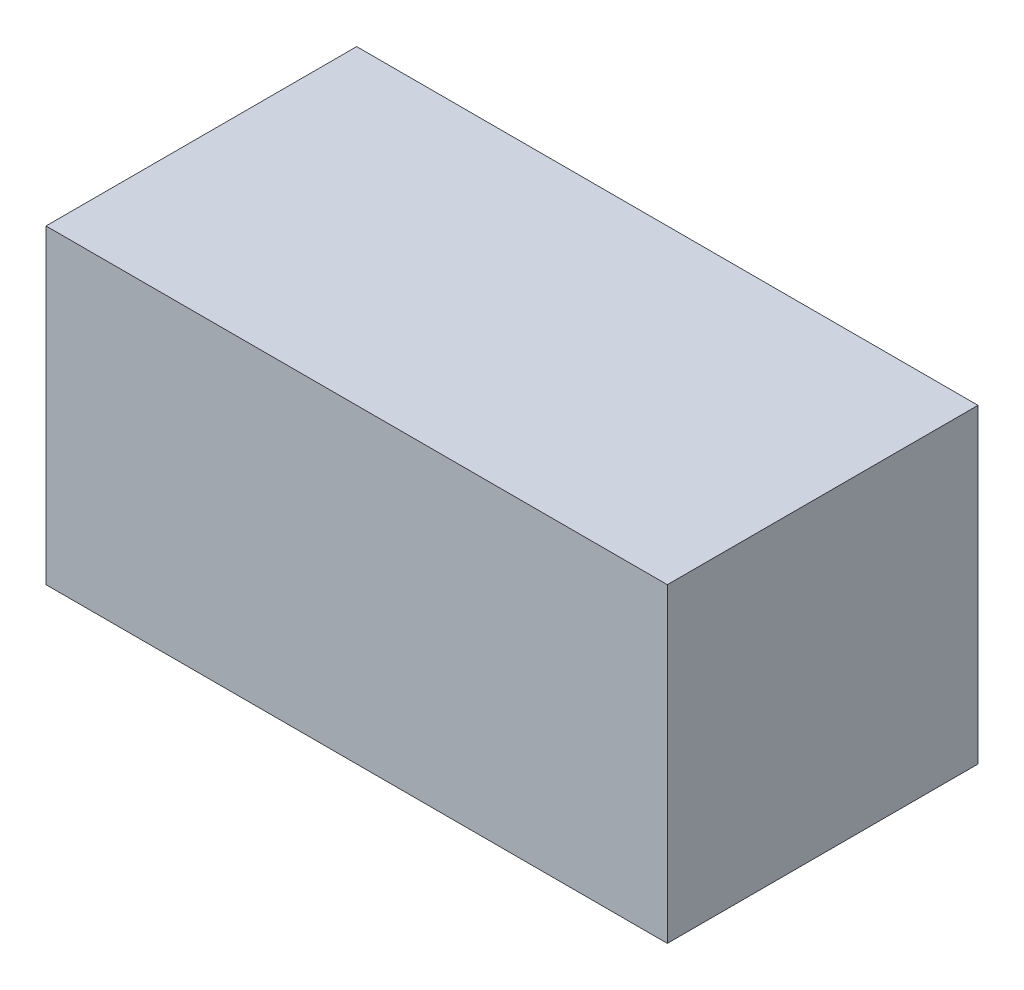
SolidWorks part; units mm, degrees
material "ｺﾝｸﾘｰﾄ"
ref_plane "正面" through (0, 0, 0) normal (0, 0, 1) x (1, 0, 0)
ref_plane "平面" through (0, 0, 0) normal (0, 1, 0) x (1, 0, 0)
ref_plane "右側面" through (0, 0, 0) normal (1, 0, 0) x (0, 0, -1)
sketch "ｽｹｯﾁ1" plane through (0, 0, 0) normal (0, 1, 0) x (1, 0, 0)
  line L5 (-150, 75) -> (150, 75)
  line L6 (-150, 75) -> (-150, -75)
  line L7 (-150, -75) -> (150, -75)
  line L8 (150, 75) -> (150, -75)
  line L9 (-150, 75) -> (150, -75) construction
  line L10 (-150, -75) -> (150, 75) construction
  point P0 (0, 0)
  dimension "D1" = 300
  dimension "D2" = 150
extrude "ﾎﾞｽ - 押し出し1" add sketch "ｽｹｯﾁ1" along normal blind 150
